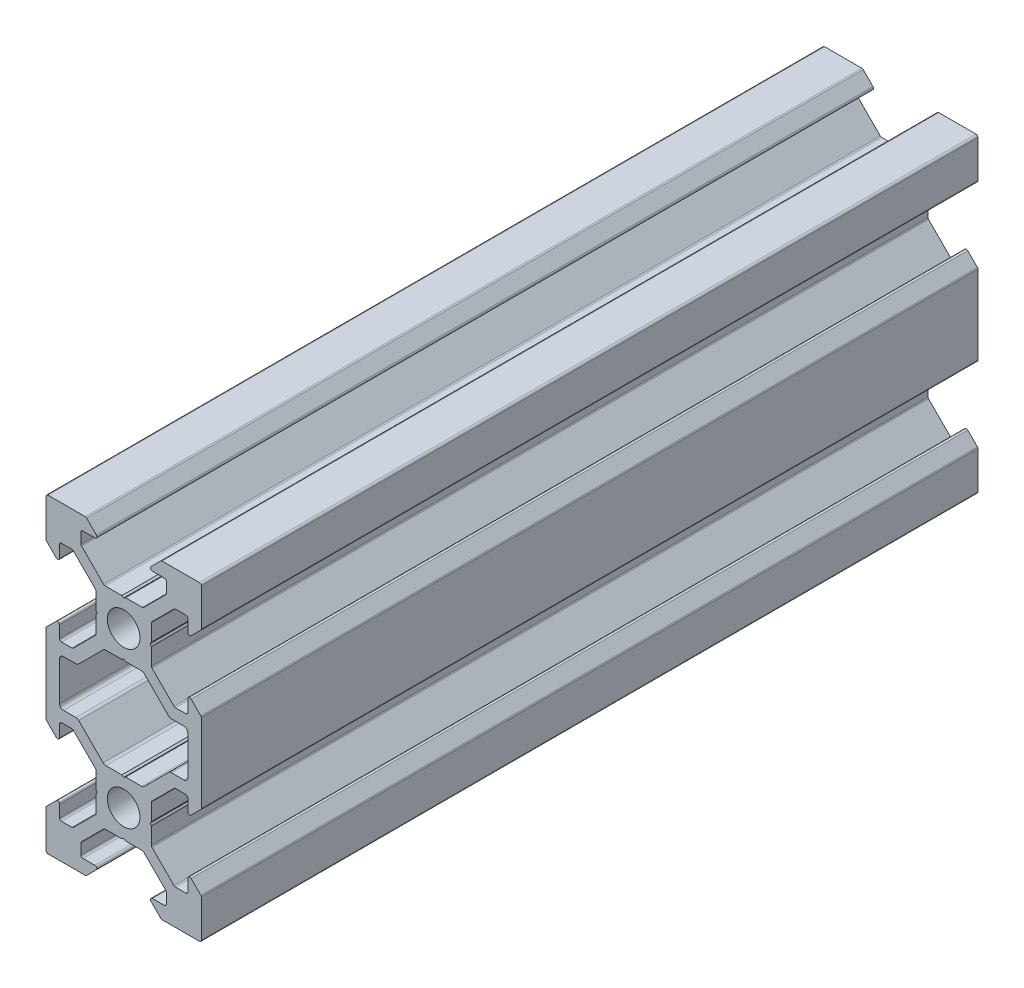
SolidWorks part; units mm, degrees
ref_plane "Front Plane" through (0, 0, 0) normal (0, 0, 1) x (1, 0, 0)
ref_plane "Top Plane" through (0, 0, 0) normal (0, 1, 0) x (1, 0, 0)
ref_plane "Right Plane" through (0, 0, 0) normal (1, 0, 0) x (0, 0, -1)
sketch "Sketch1" plane through (0, 0, 0) normal (0, 0, 1) x (1, 0, 0)
  line L0 (3.5607, 3.5607) -> (10.6317, 10.6317) construction
  line L1 (2.5, -3.5607) -> (-2.5, -3.5607)
  line L2 (3.5607, -2.5) -> (3.5607, 2.5)
  line L3 (2.5, 3.5607) -> (-2.5, 3.5607)
  line L4 (-3.5607, -2.5) -> (-3.5607, 2.5)
  line L5 (3.5607, -3.5607) -> (-3.5607, 3.5607) construction
  line L6 (3.5607, 3.5607) -> (-3.5607, -3.5607) construction
  line L7 (2.5, 3.5607) -> (5.5, 6.5607)
  line L8 (5.5, 6.5607) -> (5.5, 8.2521)
  line L9 (5.5, 8.2521) -> (3.1, 8.2521)
  line L10 (3.1, 8.2521) -> (4.8479, 10)
  line L11 (4.8479, 10) -> (10, 10)
  line L12 (3.5607, 2.5) -> (6.5607, 5.5)
  line L13 (6.5607, 5.5) -> (8.2521, 5.5)
  line L14 (8.2521, 5.5) -> (8.2521, 3.1)
  line L15 (8.2521, 3.1) -> (10, 4.8479)
  line L16 (10, 4.8479) -> (10, 10)
  line L17 (0, -55) -> (0, 55) construction
  line L18 (-3.5607, 3.5607) -> (-10.6317, 10.6317) construction
  line L19 (-10, 4.8479) -> (-10, 10)
  line L20 (-8.2521, 3.1) -> (-10, 4.8479)
  line L21 (-8.2521, 5.5) -> (-8.2521, 3.1)
  line L22 (-6.5607, 5.5) -> (-8.2521, 5.5)
  line L23 (-3.5607, 2.5) -> (-6.5607, 5.5)
  line L24 (-4.8479, 10) -> (-10, 10)
  line L25 (-3.1, 8.2521) -> (-4.8479, 10)
  line L26 (-5.5, 8.2521) -> (-3.1, 8.2521)
  line L27 (-5.5, 6.5607) -> (-5.5, 8.2521)
  line L28 (-2.5, 3.5607) -> (-5.5, 6.5607)
  line L29 (-8.2521, -7) -> (-5.9393, -7)
  line L30 (55, 0) -> (-55, 0) construction
  line L31 (-3.5607, -3.5607) -> (-10.6317, -10.6317) construction
  line L32 (3.5607, -3.5607) -> (10.6317, -10.6317) construction
  line L33 (-2.5, -3.5607) -> (-5.5, -6.5607)
  line L34 (-5.5, -6.5607) -> (-5.9393, -7)
  line L35 (5.5, -6.5607) -> (5.9393, -7)
  line L36 (8.2521, -7) -> (5.9393, -7)
  line L37 (-12.2633, -10) -> (14.5346, -10) construction
  line L38 (-3.5607, -2.5) -> (-6.5607, -5.5)
  line L39 (-6.5607, -5.5) -> (-8.2521, -5.5)
  line L40 (-8.2521, -5.5) -> (-8.2521, -3.1)
  line L41 (-8.2521, -3.1) -> (-10, -4.8479)
  line L42 (-10, -4.8479) -> (-10, -7)
  line L43 (10, -4.8479) -> (10, -7)
  line L44 (8.2521, -3.1) -> (10, -4.8479)
  line L45 (8.2521, -5.5) -> (8.2521, -3.1)
  line L46 (6.5607, -5.5) -> (8.2521, -5.5)
  line L47 (3.5607, -2.5) -> (6.5607, -5.5)
  line L48 (-3.5607, -23.5607) -> (-10.6317, -30.6317) construction
  line L49 (3.5607, -23.5607) -> (-3.5607, -16.4393) construction
  line L50 (3.5607, -16.4393) -> (-3.5607, -23.5607) construction
  line L51 (3.5607, -23.5607) -> (10.6317, -30.6317) construction
  line L52 (2.5, -3.5607) -> (5.5, -6.5607)
  line L53 (2.5, -16.4393) -> (5.5, -13.4393)
  line L54 (3.5607, -17.5) -> (6.5607, -14.5)
  line L55 (6.5607, -14.5) -> (8.2521, -14.5)
  line L56 (8.2521, -14.5) -> (8.2521, -16.9)
  line L57 (8.2521, -16.9) -> (10, -15.1521)
  line L58 (10, -15.1521) -> (10, -13)
  line L59 (-10, -15.1521) -> (-10, -13)
  line L60 (-8.2521, -16.9) -> (-10, -15.1521)
  line L61 (-8.2521, -14.5) -> (-8.2521, -16.9)
  line L62 (-6.5607, -14.5) -> (-8.2521, -14.5)
  line L63 (-3.5607, -17.5) -> (-6.5607, -14.5)
  line L64 (8.2521, -13) -> (5.9393, -13)
  line L65 (5.5, -13.4393) -> (5.9393, -13)
  line L66 (-5.5, -13.4393) -> (-5.9393, -13)
  line L67 (-2.5, -16.4393) -> (-5.5, -13.4393)
  line L68 (-8.2521, -13) -> (-5.9393, -13)
  line L69 (-2.5, -23.5607) -> (-5.5, -26.5607)
  line L70 (-5.5, -26.5607) -> (-5.5, -28.2521)
  line L71 (-5.5, -28.2521) -> (-3.1, -28.2521)
  line L72 (-3.1, -28.2521) -> (-4.8479, -30)
  line L73 (-4.8479, -30) -> (-10, -30)
  line L74 (-3.5607, -22.5) -> (-6.5607, -25.5)
  line L75 (-6.5607, -25.5) -> (-8.2521, -25.5)
  line L76 (-8.2521, -25.5) -> (-8.2521, -23.1)
  line L77 (-8.2521, -23.1) -> (-10, -24.8479)
  line L78 (-10, -24.8479) -> (-10, -30)
  line L79 (10, -24.8479) -> (10, -30)
  line L80 (8.2521, -23.1) -> (10, -24.8479)
  line L81 (8.2521, -25.5) -> (8.2521, -23.1)
  line L82 (6.5607, -25.5) -> (8.2521, -25.5)
  line L83 (3.5607, -22.5) -> (6.5607, -25.5)
  line L84 (4.8479, -30) -> (10, -30)
  line L85 (3.1, -28.2521) -> (4.8479, -30)
  line L86 (5.5, -28.2521) -> (3.1, -28.2521)
  line L87 (5.5, -26.5607) -> (5.5, -28.2521)
  line L88 (2.5, -23.5607) -> (5.5, -26.5607)
  line L89 (-3.5607, -17.5) -> (-3.5607, -22.5)
  line L90 (2.5, -23.5607) -> (-2.5, -23.5607)
  line L91 (3.5607, -17.5) -> (3.5607, -22.5)
  line L92 (2.5, -16.4393) -> (-2.5, -16.4393)
  line L93 (-10, -7) -> (-10, -13)
  line L94 (-8.2521, -13) -> (-8.2521, -7)
  line L95 (8.2521, -13) -> (8.2521, -7)
  line L96 (10, -7) -> (10, -13)
  circle A0 centre (0, 0) radius 2.1
  circle A1 centre (0, -20) radius 2.1
  point P0 (0, 0)
  point P102 (0, -20)
  dimension "D10" = 4.2
  dimension "D11" = 4.2
  dimension "D1" = 1.5
  dimension "D2" = 10
  dimension "D3" = 20
  dimension "D4" = 6.2
  dimension "D5" = 11
  dimension "D6" = 45
  dimension "D7" = 1.5
  dimension "D8" = 10
  dimension "D9" = 5
extrude "Boss-Extrude1" add sketch "Sketch1" along normal blind 100
fillet "Fillet1" radius 0.25 64 edges at (5.5, 6.5607, 50) (5.5, 8.2521, 50) (3.1, 8.2521, 50) (4.8479, 10, 50) (10, 10, 50) (10, 4.8479, 50) (8.2521, 3.1, 50) (8.2521, 5.5, 50) (6.5607, 5.5, 50) (3.5607, 2.5, 50) (3.5607, -2.5, 50) (6.5607, -5.5, 50) (8.2521, -5.5, 50) (8.2521, -3.1, 50) (10, -4.8479, 50) (10, -15.1521, 50) (8.2521, -16.9, 50) (8.2521, -14.5, 50) (6.5607, -14.5, 50) (3.5607, -17.5, 50) (3.5607, -22.5, 50) (6.5607, -25.5, 50) (8.2521, -25.5, 50) (8.2521, -23.1, 50) (10, -24.8479, 50) (10, -30, 50) (4.8479, -30, 50) (3.1, -28.2521, 50) (5.5, -28.2521, 50) (5.5, -26.5607, 50) (2.5, -23.5607, 50) (-2.5, -23.5607, 50) (-5.5, -26.5607, 50) (-5.5, -28.2521, 50) (-3.1, -28.2521, 50) (-4.8479, -30, 50) (-10, -30, 50) (-10, -24.8479, 50) (-8.2521, -23.1, 50) (-8.2521, -25.5, 50) (-6.5607, -25.5, 50) (-3.5607, -22.5, 50) (-3.5607, -17.5, 50) (-6.5607, -14.5, 50) (-8.2521, -14.5, 50) (-8.2521, -16.9, 50) (-10, -15.1521, 50) (-10, -4.8479, 50) (-8.2521, -3.1, 50) (-8.2521, -5.5, 50) (-6.5607, -5.5, 50) (-3.5607, -2.5, 50) (-3.5607, 2.5, 50) (-6.5607, 5.5, 50) (-8.2521, 5.5, 50) (-8.2521, 3.1, 50) (-10, 4.8479, 50) (-10, 10, 50) (-4.8479, 10, 50) (-5.5, 8.2521, 50) (-5.5, 6.5607, 50) (-2.5, 3.5607, 50) (2.5, 3.5607, 50) (-3.1, 8.2521, 50)
fillet "Fillet2" radius 0.5 12 edges at (-5.9393, -7, 50) (-8.2521, -7, 50) (-8.2521, -13, 50) (-5.9393, -13, 50) (-2.5, -16.4393, 50) (2.5, -16.4393, 50) (8.2521, -7, 50) (5.9393, -7, 50) (2.5, -3.5607, 50) (-2.5, -3.5607, 50) (5.9393, -13, 50) (8.2521, -13, 50)
sketch "Sketch2" plane through (0, 0, 100) normal (0, 0, 1) x (1, 0, 0)
  line L4 (0, 3.5607) -> (0, 3.1447) construction
  line L5 (2.3964, 3.5607) -> (-2.3964, 3.5607) construction
  line L6 (0, 3.399) -> (-0.2423, 3.5607)
  line L7 (0, 3.399) -> (0.2423, 3.5607)
  line L8 (-0.2423, 3.5607) -> (0.2423, 3.5607)
  line L9 (55, 0) -> (-55, 0) construction
  line L10 (0, -3.5607) -> (0, -3.1447) construction
  line L11 (0, -3.399) -> (0.2423, -3.5607)
  line L12 (0, -3.399) -> (-0.2423, -3.5607)
  line L13 (-0.2423, -3.5607) -> (0.2423, -3.5607)
  line L14 (0, 0) -> (-4.0856, 4.0856) construction
  line L15 (-8.2521, -10) -> (4.1581, -10) construction
  line L16 (-8.2521, -7.5) -> (-8.2521, -12.5) construction
  line L17 (3.5607, 0) -> (3.1447, 0) construction
  line L18 (3.5607, 0.2423) -> (3.5607, -0.2423)
  line L19 (3.399, 0) -> (3.5607, 0.2423)
  line L20 (3.399, 0) -> (3.5607, -0.2423)
  line L21 (-3.5607, 0) -> (-3.1447, 0) construction
  line L22 (-3.5607, 0.2423) -> (-3.5607, -0.2423)
  line L23 (-3.399, 0) -> (-3.5607, -0.2423)
  line L24 (-3.399, 0) -> (-3.5607, 0.2423)
  line L25 (-3.5607, -20) -> (-3.1447, -20) construction
  line L26 (3.5607, -20) -> (3.1447, -20) construction
  line L27 (0, -20) -> (-4.0856, -24.0856) construction
  line L28 (0, -16.4393) -> (0, -16.8553) construction
  line L29 (0, -23.5607) -> (0, -23.1447) construction
  line L30 (-3.399, -20) -> (-3.5607, -20.2423)
  line L31 (-3.399, -20) -> (-3.5607, -19.7577)
  line L32 (-3.5607, -20.2423) -> (-3.5607, -19.7577)
  line L33 (3.399, -20) -> (3.5607, -19.7577)
  line L34 (3.399, -20) -> (3.5607, -20.2423)
  line L35 (3.5607, -20.2423) -> (3.5607, -19.7577)
  line L36 (-0.2423, -16.4393) -> (0.2423, -16.4393)
  line L37 (0, -16.601) -> (-0.2423, -16.4393)
  line L38 (0, -16.601) -> (0.2423, -16.4393)
  line L39 (-0.2423, -23.5607) -> (0.2423, -23.5607)
  line L40 (0, -23.399) -> (0.2423, -23.5607)
  line L41 (0, -23.399) -> (-0.2423, -23.5607)
extrude "Cut-Extrude1" cut sketch "Sketch2" against normal through all
